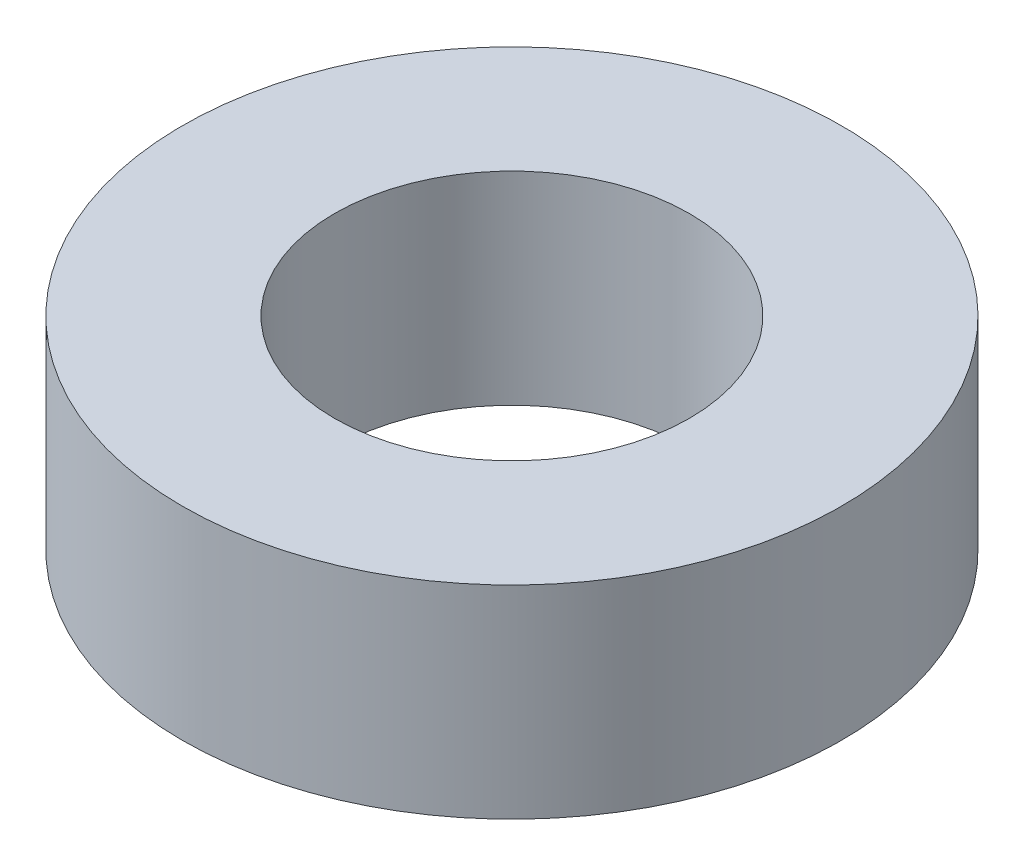
SolidWorks part; units mm, degrees
ref_plane "Front" through (0, 0, 0) normal (0, 0, 1) x (1, 0, 0)
ref_plane "Top" through (0, 0, 0) normal (0, 1, 0) x (1, 0, 0)
ref_plane "Right" through (0, 0, 0) normal (1, 0, 0) x (0, 0, -1)
sketch "Sketch1" plane through (0, 0, 0) normal (0, 1, 0) x (1, 0, 0)
  circle A0 centre (0, 0) radius 3.5
  circle A1 centre (0, 0) radius 6.5
  dimension "D1" = 7
  dimension "D2" = 13
extrude "Boss-Extrude1" add sketch "Sketch1" along normal blind 4
